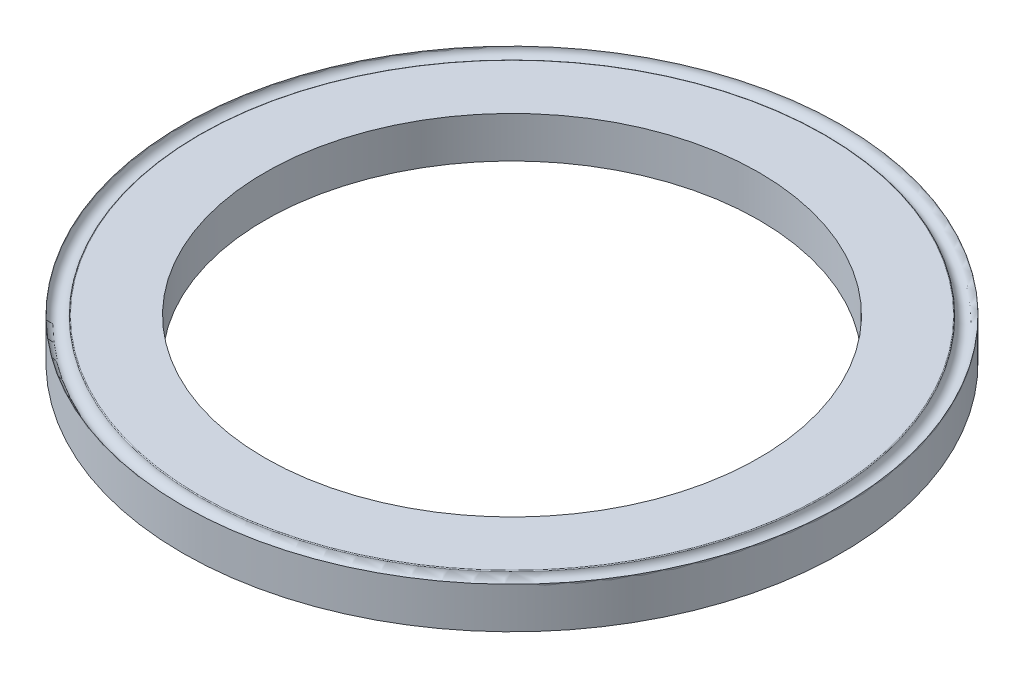
SolidWorks part; units mm, degrees
material "Chrome Stainless Steel"
ref_plane "Front Plane" through (0, 0, 0) normal (0, 0, 1) x (1, 0, 0)
ref_plane "Top Plane" through (0, 0, 0) normal (0, 1, 0) x (1, 0, 0)
ref_plane "Right Plane" through (0, 0, 0) normal (1, 0, 0) x (0, 0, -1)
sketch "DiaProfileS" plane through (0, 0, 0) normal (0, 1, 0) x (1, 0, 0)
  circle A0 centre (0, 0) radius 3
  circle A1 centre (0, 0) radius 4
  dimension "InnerDia" = 6
  dimension "Width" = 1
extrude "DiaProfile" add sketch "DiaProfileS" along normal mid plane 0.5
sketch "CrimpS" plane through (0, 0, 0) normal (0, 0, 1) x (1, 0, 0)
  line L0 (4, 0.25) -> (-4, 0.25) construction
  line L1 (-4, 0.25) -> (-4, -0.25) construction
  line L3 (-4, 0.25) -> (-3.7905, 0.25)
  arc A0 (-4, 0.25) -> (-3.8004, 0.2409) centre (-3.9, 0.25) ccw
  arc A2 (-3.8004, 0.2409) -> (-3.7905, 0.25) centre (-3.7905, 0.24) cw
  dimension "Dia" = 0.2
  dimension "Fillet" = 0.01
revolve "Crimp" cut sketch "CrimpS" angle 360 about axis through (0, 0.25, 0) along (0, -1, 0)
